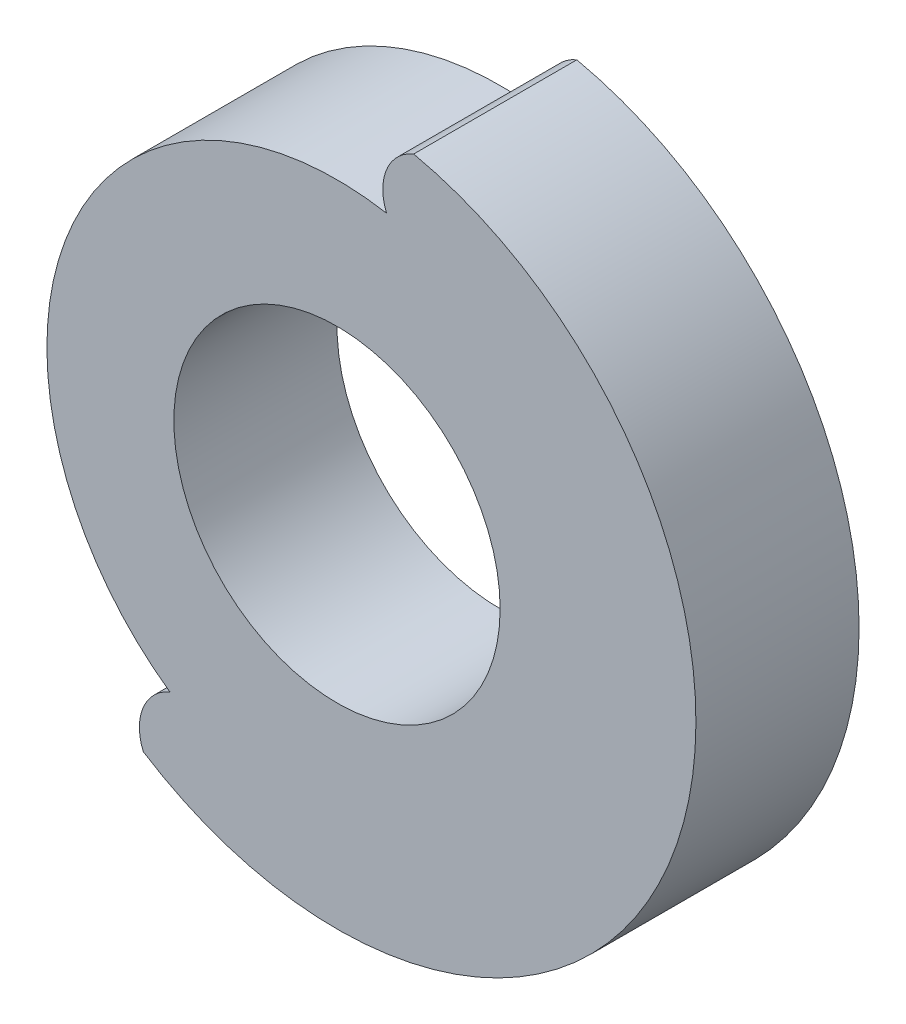
SolidWorks part; units mm, degrees
ref_plane "Front Plane" through (0, 0, 0) normal (0, 0, 1) x (1, 0, 0)
ref_plane "Top Plane" through (0, 0, 0) normal (0, 1, 0) x (1, 0, 0)
ref_plane "Right Plane" through (0, 0, 0) normal (1, 0, 0) x (0, 0, -1)
sketch "Sketch1" plane through (0, 0, 0) normal (0, 0, 1) x (1, 0, 0)
  circle A0 centre (0, 0) radius 6
  circle A1 centre (0, 0) radius 13.2
extrude "Boss-Extrude1" add sketch "Sketch1" along normal blind 6
sketch "Sketch2" plane through (0, 0, 6) normal (0, 0, 1) x (1, 0, 0)
  line L0 (0, 0) -> (0, 15.2) construction
  line L1 (-1.8199, 15.2) -> (0, 0) construction
  line L2 (1.8199, 15.2) -> (0, 0) construction
  arc A0 (-1.8199, 12) -> (1.8199, 12) centre (0, 0) cw
  arc A1 (-2.8199, 12.8953) -> (2.8199, 12.8953) centre (0, 0) cw
  arc A2 (-1.8199, 10.512) -> (1.8199, 10.512) centre (0, 0) cw
  arc A3 (-2.8199, 12.8953) -> (-1.8199, 10.512) centre (-3.5115, 11.2036) cw
  arc A4 (2.8199, 12.8953) -> (1.8199, 10.512) centre (3.5115, 11.2036) ccw
extrude "Cut-Extrude1" cut sketch "Sketch2" against normal through all contours A1 A4 A2 A3
sketch "Sketch3" plane through (0, 0, 0) normal (0, 0, 1) x (1, 0, 0)
  circle A0 centre (0, 0) radius 6
  circle A1 centre (0, 0) radius 13.2
extrude "Boss-Extrude2" add sketch "Sketch3" along normal blind 6
sketch "Sketch4" plane through (0, 0, 6) normal (0, 0, 1) x (1, 0, 0)
  line L0 (0, 0) -> (0, 15.2) construction
  line L1 (-1.8199, 15.2) -> (0, 0) construction
  line L2 (1.8199, 15.2) -> (0, 0) construction
  arc A0 (-1.8199, 12) -> (1.8199, 12) centre (0, 0) cw
  arc A1 (-2.8199, 12.8953) -> (2.8199, 12.8953) centre (0, 0) cw
  arc A2 (-1.8199, 10.512) -> (1.8199, 10.512) centre (0, 0) cw
  arc A3 (-2.8199, 12.8953) -> (-1.8199, 10.512) centre (-3.5115, 11.2036) cw
  arc A4 (2.8199, 12.8953) -> (1.8199, 10.512) centre (3.5115, 11.2036) ccw
extrude "Cut-Extrude2" cut sketch "Sketch4" against normal through all contours A1 A4 A2 A3
pattern_circular "CirPattern2" count 10 every 15 of "Cut-Extrude2"
